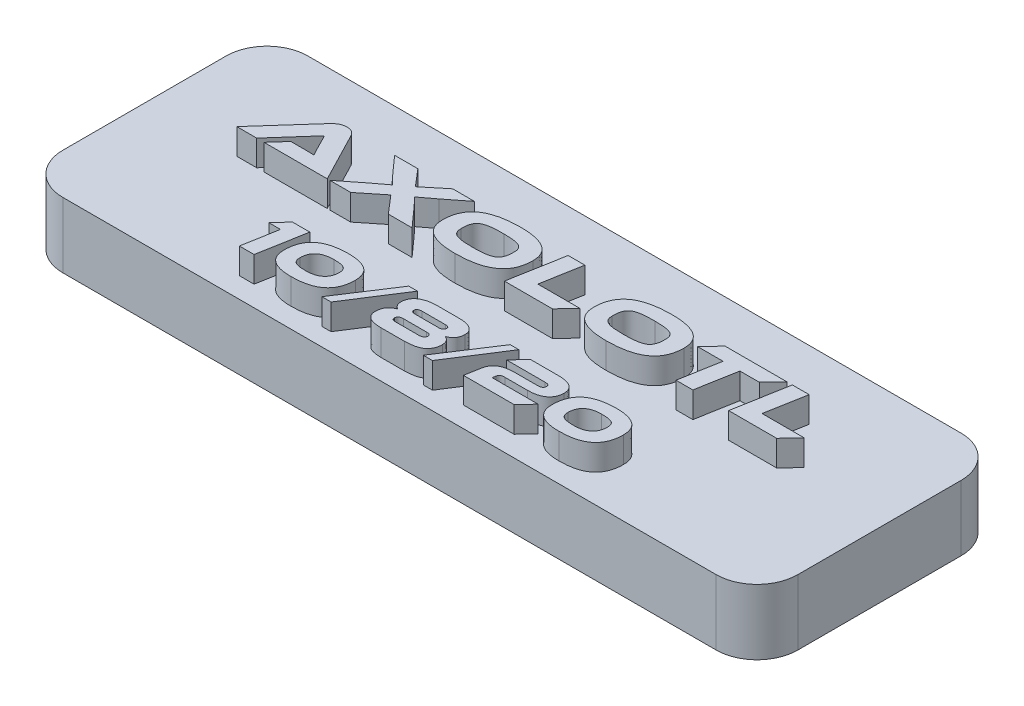
SolidWorks part; units mm, degrees
ref_plane "Front Plane" through (0, 0, 0) normal (0, 0, 1) x (1, 0, 0)
ref_plane "Top Plane" through (0, 0, 0) normal (0, 1, 0) x (1, 0, 0)
ref_plane "Right Plane" through (0, 0, 0) normal (1, 0, 0) x (0, 0, -1)
sketch "Sketch1" plane through (0, 0, 0) normal (0, 1, 0) x (1, 0, 0)
  line L1 (-28.575, 9.525) -> (28.575, 9.525)
  line L2 (-28.575, 9.525) -> (-28.575, -9.525)
  line L3 (-28.575, -9.525) -> (28.575, -9.525)
  line L4 (28.575, 9.525) -> (28.575, -9.525)
  line L5 (-28.575, 9.525) -> (28.575, -9.525) construction
  line L6 (-28.575, -9.525) -> (28.575, 9.525) construction
  point P0 (0, 0)
  dimension "D1" = 57.15
  dimension "D2" = 19.05
extrude "Boss-Extrude1" add sketch "Sketch1" along normal up to surface (5.08 mm away)
fillet "Fillet1" radius 3.175 4 edges at (-28.575, 2.54, 9.525) (-28.575, 2.54, -9.525) (28.575, 2.54, 9.525) (28.575, 2.54, -9.525)
sketch "Sketch3" plane through (0, 5.08, 0) normal (0, 1, 0) x (1, 0, 0)
  line L0 (28.575, -7.9375) -> (-28.575, -7.9375) construction
  line L1 (28.575, -6.35) -> (28.575, 6.35) construction
  line L2 (-28.575, 6.35) -> (-28.575, -6.35) construction
  line L3 (28.575, 0) -> (-28.575, 0) construction
  line L5 (-25.4, -9.525) -> (25.4, -9.525) construction
  line L6 (25.4, 9.525) -> (-25.4, 9.525) construction
  text T0 "Axolotl" font "Ethnocentric Rg" height in points 16
  text T1 "10/8/20\r\n" font "Ethnocentric Rg" height in points 14
  point P8 (-28.575, 0)
  dimension "D1" = 1.5875
extrude "Boss-Extrude2" add sketch "Sketch3" along normal blind 2
sketch "Sketch4" plane through (0, 0, 0) normal (0, -1, 0) x (1, 0, 0)
  line L0 (25.4, 0) -> (-25.4, 0) construction
  circle A0 centre (-25.4, 0) radius 0.9
  circle A1 centre (25.4, 0) radius 0.9
  point P3 (0, 0)
  dimension "D2" = 1.8
  dimension "D1" = 50.8
extrude "Cut-Extrude1" cut sketch "Sketch4" against normal blind 4
